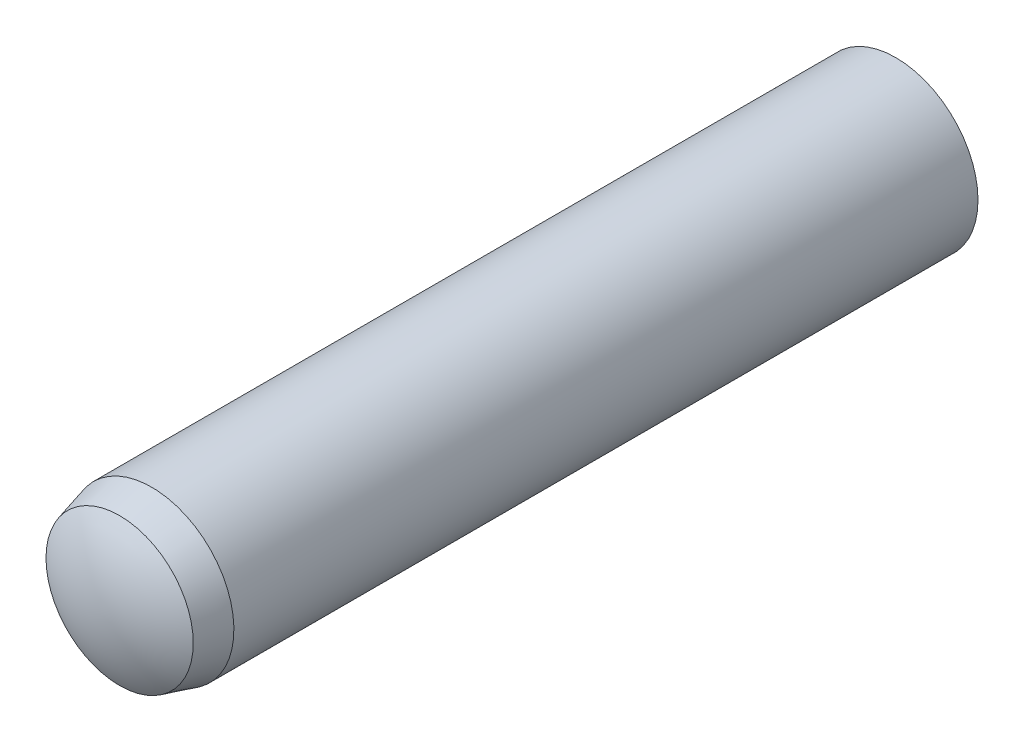
SolidWorks part; units mm, degrees
ref_plane "Front Plane" through (0, 0, 0) normal (0, 0, 1) x (1, 0, 0)
ref_plane "Top Plane" through (0, 0, 0) normal (0, 1, 0) x (1, 0, 0)
ref_plane "Right Plane" through (0, 0, 0) normal (1, 0, 0) x (0, 0, -1)
sketch "Sketch1" plane through (0, 0, 0) normal (0, 0, 1) x (1, 0, 0)
  circle A0 centre (0, 0) radius 2
  point P3 (0, 2)
  dimension "Diameter" = 4
sketch "Sketch2" plane through (0, 0, 0) normal (1, 0, 0) x (0, 0, -1)
  line L0 (-10, 0) -> (10, 0) construction
  line L1 (-10, 0) -> (-10, 2) construction
  line L2 (-10, 2) -> (10, 2)
  line L3 (10, 2) -> (10, 0) construction
  line L4 (-9.48, 1.791) -> (-8.7, 2)
  arc A0 (-10, 0) -> (-9.48, 1.791) centre (-6.6557, 0) cw
  arc A1 (10, 0) -> (9.4, 2) centre (6.3667, 0) ccw
  point P2 (0, 0)
  point P11 (-6, 0)
  point P13 (6, 0)
  dimension "Length" = 20
  dimension "D1" = 15
  dimension "D2" = 0.6
  dimension "D3" = 1.3
  dimension "D4" = 0.78
  dimension "D5" = 4
  dimension "D6" = 4
sketch "Sketch3" plane through (0, 0, 0) normal (1, 0, 0) x (0, 0, -1)
  line L0 (-10, 0) -> (10, 0) construction
  line L1 (-9.48, 1.791) -> (-8.7, 2) construction
  line L2 (-10, 0) -> (10, 0)
  line L3 (-9.48, 1.791) -> (-8.7, 2)
  line L4 (-8.7, 2) -> (9.4, 2)
  arc A0 (10, 0) -> (9.4, 2) centre (6.3667, 0) ccw construction
  arc A1 (-9.48, 1.791) -> (-10, 0) centre (-6.6557, 0) ccw construction
  arc A2 (10, 0) -> (9.4, 2) centre (6.3667, 0) ccw
  arc A3 (-9.48, 1.791) -> (-10, 0) centre (-6.6557, 0) ccw
revolve "Revolve1" add sketch "Sketch3" angle 360 about L2
equation "\"D2@Sketch2\" = \"Diameter@Sketch1\" * .15"
equation "\"D3@Sketch2\" = \"Diameter@Sketch1\" * .325"
equation "\"D4@Sketch2\" = \"D3@Sketch2\" * .6"
equation "\"D5@Sketch2\"=\"Diameter@Sketch1\""
equation "\"D6@Sketch2\"=\"D5@sketch2\""
